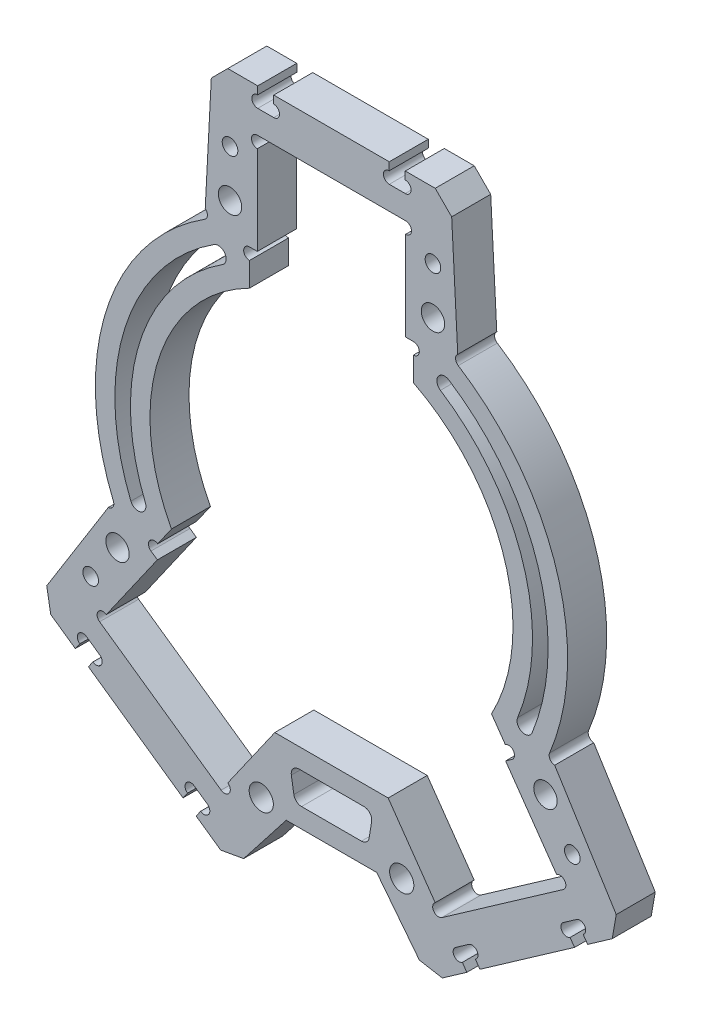
SolidWorks part; units mm, degrees
ref_plane "前视基准面" through (0, 0, 0) normal (0, 0, 1) x (1, 0, 0)
ref_plane "上视基准面" through (0, 0, 0) normal (0, 1, 0) x (1, 0, 0)
ref_plane "右视基准面" through (0, 0, 0) normal (1, 0, 0) x (0, 0, -1)
sketch "草图1" plane through (0, 0, 0) normal (0, 0, 1) x (1, 0, 0)
  line L0 (-2.5, 23.8) -> (-2.1208, 23.8) construction
  line L1 (-2.5, 23.8) -> (-3.9, 25.8) construction
  line L2 (-3.9, 25.8) -> (3.9, 25.8) construction
  line L3 (3.9, 25.8) -> (2.5, 23.8) construction
  line L4 (2.5, 23.8) -> (2.1208, 23.8) construction
  line L5 (-3.5, 25.2286) -> (3.5, 25.2286) construction
  line L6 (-9.5, 38.2286) -> (9.5, 38.2286)
  line L7 (-15, 49.2286) -> (15, 49.2286)
  line L8 (-15, 49.2286) -> (-16.2421, 25.5284)
  line L9 (0, 38.2286) -> (0, 49.2286) construction
  line L10 (29.709, -25.866) -> (14.1451, -36.764)
  line L11 (0, 0) -> (9.5, 38.2286) construction
  line L12 (0, 0) -> (14.1451, -36.764) construction
  line L13 (-40.5236, -31.722) -> (-27.9472, -11.5956)
  line L15 (15.9491, -48.9293) -> (40.5236, -31.722)
  line L20 (9.5, 38.2286) -> (9.5, 21.2286)
  line L23 (19.9582, -11.9405) -> (29.709, -25.866)
  line L25 (-19.9582, -11.9405) -> (-29.709, -25.866)
  line L26 (-29.709, -25.866) -> (-14.1451, -36.764)
  line L28 (-15.9491, -48.9293) -> (-40.5236, -31.722)
  line L30 (-9.5, 38.2286) -> (-9.5, 21.2286)
  line L36 (15, 49.2286) -> (16.2421, 25.5284)
  line L37 (27.9472, -11.5956) -> (40.5236, -31.722)
  line L38 (-14.1451, -36.764) -> (-7.2621, -26.9342)
  line L39 (14.1451, -36.764) -> (7.2621, -26.9342)
  line L40 (-5.7961, -35.9342) -> (5.7961, -35.9342)
  line L41 (-7.2621, -26.9342) -> (7.2621, -26.9342)
  line L42 (-15.9491, -48.9293) -> (-5.7961, -35.9342)
  line L43 (15.9491, -48.9293) -> (5.7961, -35.9342)
  line L44 (-28.2363, -40.3257) -> (-21.927, -31.315) construction
  circle A0 centre (0, 0) radius 22.5 construction
  circle A1 centre (0, 24.88) radius 2.38 construction
  arc A6 (19.9582, -11.9405) -> (9.5, 21.2286) centre (0, 0) ccw
  arc A7 (-9.5, 21.2286) -> (-19.9582, -11.9405) centre (0, 0) ccw
  arc A8 (27.9472, -11.5956) -> (16.2421, 25.5284) centre (0, 0) ccw
  arc A9 (-16.2421, 25.5284) -> (-27.9472, -11.5956) centre (0, 0) ccw
  point P12 (0, 22.5)
  point P17 (0, 38.2286)
  dimension "D1" = 45
  dimension "D2" = 4.76
  dimension "D11" = 17
  dimension "D16" = 5.5
  dimension "D17" = 30
  dimension "D21" = 12
  dimension "D15" = 7
  dimension "D20" = 3
  dimension "D3" = 2.5
  dimension "D4" = 3.9
  dimension "D5" = 2
  dimension "D6" = 1.3
  dimension "D7" = 7
  dimension "D8" = 13
  dimension "D9" = 11
  dimension "D10" = 19
  dimension "D12" = 2
  dimension "D13" = 145
  dimension "D14" = 17
  dimension "D18" = 3
  dimension "D19" = 11
  dimension "D22" = 3
  dimension "D23" = 9
extrude "凸台-拉伸1" add sketch "草图1" along normal mid plane 5
sketch "草图2" plane through (0, 0, 2.5) normal (0, 0, 1) x (1, 0, 0)
  line L0 (0, 49.2286) -> (0, 38.2286) construction
  line L1 (15, 49.2286) -> (-15, 49.2286) construction
  line L2 (-9.5, 38.2286) -> (9.5, 38.2286) construction
  line L3 (9.45, 41.2286) -> (7.4, 41.2286)
  line L4 (-9.45, 46.2286) -> (-7.4, 46.2286)
  line L5 (-9.45, 46.2286) -> (-9.45, 41.2286)
  line L6 (-9.45, 41.2286) -> (-7.4, 41.2286)
  line L7 (-7.4, 46.2286) -> (-7.4, 41.2286)
  line L12 (7.4, 46.2286) -> (7.4, 41.2286)
  line L13 (9.45, 46.2286) -> (7.4, 46.2286)
  line L14 (9.45, 46.2286) -> (9.45, 41.2286)
  line L15 (34.2566, -32.4479) -> (31.3887, -28.3522)
  line L16 (34.2566, -32.4479) -> (32.5773, -33.6238)
  line L17 (32.5773, -33.6238) -> (29.7095, -29.528)
  line L18 (31.3887, -28.3522) -> (29.7095, -29.528)
  line L19 (15.9068, -39.1928) -> (17.586, -38.0169)
  line L20 (20.4539, -42.1127) -> (17.586, -38.0169)
  line L21 (18.7746, -43.2885) -> (20.4539, -42.1127)
  line L22 (18.7746, -43.2885) -> (15.9068, -39.1928)
  line L23 (-34.2566, -32.4479) -> (-32.5773, -33.6238)
  line L24 (-32.5773, -33.6238) -> (-29.7095, -29.528)
  line L25 (-31.3887, -28.3522) -> (-29.7095, -29.528)
  line L26 (-34.2566, -32.4479) -> (-31.3887, -28.3522)
  line L27 (-18.7746, -43.2885) -> (-15.9068, -39.1928)
  line L28 (-18.7746, -43.2885) -> (-20.4539, -42.1127)
  line L29 (-20.4539, -42.1127) -> (-17.586, -38.0169)
  line L30 (-15.9068, -39.1928) -> (-17.586, -38.0169)
  point P14 (-9.45, 43.7286)
  point P26 (0, 0)
  dimension "D1" = 5.5
  dimension "D2" = 5
  dimension "D3" = 18.9
  dimension "D4" = 2.05
  dimension "D6" = 145
  dimension "D5" = 2
extrude "切除-拉伸1" cut sketch "草图2" against normal through all
sketch "草图3" plane through (0, 0, 2.5) normal (0, 0, 1) x (1, 0, 0)
  line L0 (-9.45, 46.2286) -> (-9.45, 41.2286) construction
  line L1 (-7.4, 41.2286) -> (-7.4, 46.2286) construction
  line L2 (7.4, 46.2286) -> (7.4, 41.2286) construction
  line L3 (9.45, 41.2286) -> (9.45, 46.2286) construction
  line L4 (-31.3887, -28.3522) -> (-34.2566, -32.4479) construction
  line L5 (-32.5773, -33.6238) -> (-29.7095, -29.528) construction
  line L6 (-17.586, -38.0169) -> (-20.4539, -42.1127) construction
  line L7 (-18.7746, -43.2885) -> (-15.9068, -39.1928) construction
  line L8 (15.9068, -39.1928) -> (18.7746, -43.2885) construction
  line L9 (20.4539, -42.1127) -> (17.586, -38.0169) construction
  line L10 (29.7095, -29.528) -> (32.5773, -33.6238) construction
  line L11 (34.2566, -32.4479) -> (31.3887, -28.3522) construction
  line L12 (-9.5, 38.2286) -> (9.5, 38.2286) construction
  line L13 (-14.1451, -36.764) -> (-29.709, -25.866) construction
  line L14 (29.709, -25.866) -> (14.1451, -36.764) construction
  line L15 (-14.1451, -36.764) -> (-7.2621, -26.9342) construction
  line L16 (7.2621, -26.9342) -> (14.1451, -36.764) construction
  circle A0 centre (-9.45, 45.4786) radius 0.75
  circle A1 centre (-9.45, 41.9786) radius 0.75
  circle A2 centre (-7.4, 41.9786) radius 0.75
  circle A3 centre (-7.4, 45.4786) radius 0.75
  circle A4 centre (7.4, 45.4786) radius 0.75
  circle A5 centre (7.4, 41.9786) radius 0.75
  circle A6 centre (9.45, 41.9786) radius 0.75
  circle A7 centre (9.45, 45.4786) radius 0.75
  circle A8 centre (-9.5, 37.4786) radius 0.75
  circle A9 centre (9.5, 37.4786) radius 0.75
  circle A10 centre (-29.2788, -25.2517) radius 0.75
  circle A11 centre (29.2788, -25.2517) radius 0.75
  circle A12 centre (-31.8189, -28.9665) radius 0.75
  circle A13 centre (-30.1396, -30.1424) radius 0.75
  circle A14 centre (-33.8264, -31.8336) radius 0.75
  circle A15 centre (-32.1472, -33.0094) radius 0.75
  circle A16 centre (-18.0162, -38.6313) radius 0.75
  circle A17 centre (-20.0237, -41.4983) radius 0.75
  circle A18 centre (-16.3369, -39.8071) radius 0.75
  circle A19 centre (-18.3445, -42.6742) radius 0.75
  circle A20 centre (16.3369, -39.8071) radius 0.75
  circle A21 centre (18.3445, -42.6742) radius 0.75
  circle A22 centre (18.0162, -38.6313) radius 0.75
  circle A23 centre (20.0237, -41.4983) radius 0.75
  circle A24 centre (30.1396, -30.1424) radius 0.75
  circle A25 centre (32.1472, -33.0094) radius 0.75
  circle A26 centre (33.8264, -31.8336) radius 0.75
  circle A27 centre (31.8189, -28.9665) radius 0.75
  circle A28 centre (-13.7149, -36.1496) radius 0.75
  circle A29 centre (13.7149, -36.1496) radius 0.75
  dimension "D1" = 1.5
extrude "切除-拉伸2" cut sketch "草图3" against normal through all
sketch "草图4" plane through (0, 0, -2.5) normal (0, 0, -1) x (-1, 0, 0)
  line L0 (-9.5, 25.3286) -> (-10.5, 25.3286)
  line L1 (-9.5, 36.7286) -> (-9.5, 21.2286) construction
  line L2 (-10.5, 25.3286) -> (-10.5, 20.7522)
  line L3 (-10.5, 20.7522) -> (-9.5, 21.2286)
  line L4 (-9.5, 21.2286) -> (-9.5, 25.3286)
  line L5 (-22.3098, -15.299) -> (-23.129, -14.7254)
  line L6 (-19.9582, -11.9405) -> (-28.8486, -24.6373) construction
  line L7 (-23.129, -14.7254) -> (-20.504, -10.9766)
  line L8 (-20.504, -10.9766) -> (-19.9582, -11.9405)
  line L9 (-19.9582, -11.9405) -> (-22.3098, -15.299)
  line L10 (9.5, 38.2286) -> (-9.5, 38.2286) construction
  line L11 (-29.709, -25.866) -> (-14.1451, -36.764) construction
  line L12 (0, 49.2286) -> (0, 38.2286) construction
  line L13 (-15, 49.2286) -> (15, 49.2286) construction
  line L14 (20.504, -10.9766) -> (19.9582, -11.9405)
  line L15 (23.129, -14.7254) -> (20.504, -10.9766)
  line L16 (22.3098, -15.299) -> (23.129, -14.7254)
  line L17 (19.9582, -11.9405) -> (22.3098, -15.299)
  line L18 (10.5, 20.7522) -> (9.5, 21.2286)
  line L19 (10.5, 25.3286) -> (10.5, 20.7522)
  line L20 (9.5, 25.3286) -> (10.5, 25.3286)
  line L21 (9.5, 21.2286) -> (9.5, 25.3286)
  arc A0 (-9.5, 21.2286) -> (-19.9582, -11.9405) centre (0, 0) ccw construction
  dimension "D1" = 12.9
  dimension "D2" = 1
  dimension "D3" = 12.9
  dimension "D4" = 1
extrude "切除-拉伸3" cut sketch "草图4" against normal through all
sketch "草图5" plane through (0, 0, -2.5) normal (0, 0, -1) x (-1, 0, 0)
  line L0 (-10.5, 25.3286) -> (-10.5, 20.7522) construction
  line L1 (-20.504, -10.9766) -> (-23.129, -14.7254) construction
  line L2 (23.129, -14.7254) -> (20.504, -10.9766) construction
  line L3 (10.5, 20.7522) -> (10.5, 25.3286) construction
  circle A0 centre (-10.5, 24.5786) radius 0.75
  circle A1 centre (-22.6988, -14.111) radius 0.75
  circle A2 centre (22.6988, -14.111) radius 0.75
  circle A3 centre (10.5, 24.5786) radius 0.75
  dimension "D1" = 1.5
extrude "切除-拉伸4" cut sketch "草图5" against normal through all
sketch "草图7" plane through (0, 0, 2.5) normal (0, 0, 1) x (1, 0, 0)
  line L0 (-10.5, 20.7522) -> (-10.5, 23.8286) construction
  line L1 (-22.2686, -13.4967) -> (-20.504, -10.9766) construction
  line L2 (0, 0) -> (0, 38.2286) construction
  line L3 (-9.5, 38.2286) -> (9.5, 38.2286) construction
  arc A0 (-24.7762, -10.1041) -> (-14.5, 22.4878) centre (0, 0) cw construction
  arc A1 (-15.0419, 23.3283) -> (-25.7022, -10.4817) centre (0, 0) ccw
  arc A2 (-13.9581, 21.6474) -> (-23.8502, -9.7265) centre (0, 0) ccw
  arc A3 (-13.9581, 21.6474) -> (-15.0419, 23.3283) centre (-14.5, 22.4878) ccw
  arc A4 (-25.7022, -10.4817) -> (-23.8502, -9.7265) centre (-24.7762, -10.1041) ccw
  arc A5 (-10.5, 20.7522) -> (-20.504, -10.9766) centre (0, 0) ccw construction
  arc A6 (24.7762, -10.1041) -> (14.5, 22.4878) centre (0, 0) ccw construction
  arc A7 (15.0419, 23.3283) -> (25.7022, -10.4817) centre (0, 0) cw
  arc A8 (13.9581, 21.6474) -> (23.8502, -9.7265) centre (0, 0) cw
  arc A9 (13.9581, 21.6474) -> (15.0419, 23.3283) centre (14.5, 22.4878) cw
  arc A10 (25.7022, -10.4817) -> (23.8502, -9.7265) centre (24.7762, -10.1041) cw
  point P4 (-25.5189, 8.0461)
  point P22 (25.5189, 8.0461)
  dimension "D1" = 1
  dimension "D2" = 3.5
  dimension "D3" = 4
  dimension "D4" = 4
extrude "切除-拉伸6" cut sketch "草图7" against normal through all
sketch "草图8" plane through (0, 0, 2.5) normal (0, 0, 1) x (1, 0, 0)
  circle A0 centre (-16.6447, 26.1612) radius 0.75
  circle A1 centre (16.6447, 26.1612) radius 0.75
  circle A2 centre (-28.64, -11.883) radius 0.75
  circle A3 centre (28.64, -11.883) radius 0.75
  arc A4 (-16.2421, 25.5284) -> (-27.9472, -11.5956) centre (0, 0) ccw construction
  arc A5 (27.9472, -11.5956) -> (16.2421, 25.5284) centre (0, 0) ccw construction
  dimension "D1" = 1.5
extrude "切除-拉伸7" cut sketch "草图8" against normal through all
sketch "草图9" plane through (0, 0, 2.5) normal (0, 0, 1) x (1, 0, 0)
  line L0 (-15.2882, 43.7286) -> (15.2882, 43.7286)
  line L1 (-15, 49.2286) -> (-16.1781, 26.7484) construction
  line L2 (16.1781, 26.7484) -> (15, 49.2286) construction
  line L4 (-15.2882, 43.7286) -> (-15, 49.2286)
  line L5 (-15, 49.2286) -> (15, 49.2286)
  line L6 (15, 49.2286) -> (-15, 49.2286) construction
  line L7 (15, 49.2286) -> (15.2882, 43.7286)
  line L8 (-9.5, 38.2286) -> (9.5, 38.2286) construction
  dimension "D1" = 5.5
extrude "切除-拉伸8" cut sketch "草图9" against normal through all
sketch "草图10" plane through (0, 0, 2.5) normal (0, 0, 1) x (1, 0, 0)
  line L0 (-37.6051, -27.0514) -> (-12.5583, -44.5893)
  line L1 (-28.5946, -12.6316) -> (-40.5236, -31.722) construction
  line L2 (-15.9491, -48.9293) -> (-5.7961, -35.9342) construction
  line L3 (-12.5583, -44.5893) -> (-15.9491, -48.9293)
  line L4 (-15.9491, -48.9293) -> (-40.5236, -31.722)
  line L5 (-40.5236, -31.722) -> (-37.6051, -27.0514)
  line L6 (-29.709, -25.866) -> (-14.1451, -36.764) construction
  dimension "D1" = 5.5
extrude "切除-拉伸9" cut sketch "草图10" against normal through all
mirror "镜向1" about plane through (0, 0, 0) normal (1, 0, 0) of "切除-拉伸9"
sketch "草图11" plane through (0, 0, 2.5) normal (0, 0, 1) x (1, 0, 0)
  line L0 (-5.3351, -29.4342) -> (-4.6836, -33.4342)
  line L1 (-4.6836, -33.4342) -> (4.6836, -33.4342)
  line L2 (4.6836, -33.4342) -> (5.3351, -29.4342)
  line L3 (5.3351, -29.4342) -> (-5.3351, -29.4342)
  line L4 (0, -26.9342) -> (0, -35.9342) construction
  line L5 (-7.2621, -26.9342) -> (7.2621, -26.9342) construction
  line L6 (-5.7961, -35.9342) -> (5.7961, -35.9342) construction
  line L7 (-7.2621, -26.9342) -> (-5.7961, -35.9342) construction
  point P10 (0, -29.4342)
  point P11 (0, -33.4342)
  dimension "D1" = 2.5
  dimension "D2" = 2.5
  dimension "D3" = 1.5
extrude "切除-拉伸10" cut sketch "草图11" against normal through all
fillet "圆角1" radius 1 4 edges at (5.3351, -29.4342, 0) (4.6836, -33.4342, 0) (-4.6836, -33.4342, 0) (-5.3351, -29.4342, 0)
sketch "草图12" plane through (0, 0, 2.5) normal (0, 0, 1) x (1, 0, 0)
  line L0 (-9.5, 36.7286) -> (-9.5, 25.3286) construction
  line L3 (9.5, 38.2286) -> (-9.5, 38.2286) construction
  line L4 (-22.3098, -15.299) -> (-28.8486, -24.6373) construction
  line L5 (-29.709, -25.866) -> (-14.1451, -36.764) construction
  line L6 (0, -26.9342) -> (0, -35.9342) construction
  line L7 (-7.2621, -26.9342) -> (7.2621, -26.9342) construction
  line L8 (-5.7961, -35.9342) -> (5.7961, -35.9342) construction
  line L9 (-30.8553, -21.4011) -> (-27.4138, -16.4862) construction
  line L10 (-13, 35.2286) -> (-13, 29.2286) construction
  circle A0 centre (-13, 29.2286) radius 1.5
  circle A2 centre (-27.4138, -16.4862) radius 1.5
  circle A3 centre (13, 29.2286) radius 1.5
  circle A4 centre (27.4138, -16.4862) radius 1.5
  circle A5 centre (-13, 35.2286) radius 1
  circle A6 centre (-30.8553, -21.4011) radius 1
  circle A7 centre (30.8553, -21.4011) radius 1
  circle A8 centre (13, 35.2286) radius 1
  dimension "D1" = 3
  dimension "D3" = 9
  dimension "D2" = 3.5
  dimension "D4" = 3.5
  dimension "D5" = 9
  dimension "D6" = 2
  dimension "D7" = 6
extrude "切除-拉伸11" cut sketch "草图12" against normal through all
chamfer "倒角1" distance 2 angle 45 6 edges at (37.6051, -27.0514, 0) (12.5583, -44.5893, 0) (-12.5583, -44.5893, 0) (-37.6051, -27.0514, 0) (-15.2882, 43.7286, 0) (15.2882, 43.7286, 0)
sketch "草图13" plane through (0, 0, -2.5) normal (0, 0, -1) x (-1, 0, 0)
  line L0 (0, -29.4342) -> (0, -33.4342) construction
  line L1 (-4.1591, -29.4342) -> (4.1591, -29.4342) construction
  line L2 (3.8333, -33.4342) -> (-3.8333, -33.4342) construction
  circle A0 centre (-9, -35) radius 1.55
  circle A2 centre (9, -35) radius 1.55
  dimension "D1" = 3.1
  dimension "D2" = 35
  dimension "D3" = 9
extrude "切除-拉伸12" cut sketch "草图13" against normal through all
